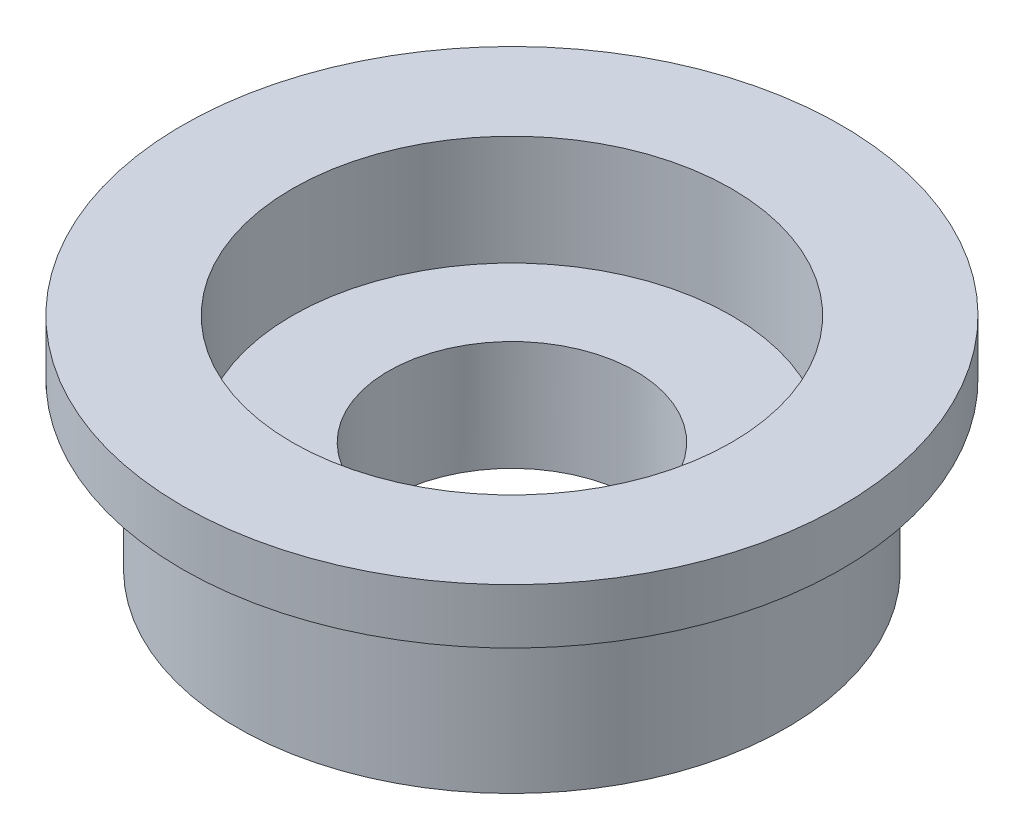
SolidWorks part; units mm, degrees
ref_plane "前视基准面" through (0, 0, 0) normal (0, 0, 1) x (1, 0, 0)
ref_plane "上视基准面" through (0, 0, 0) normal (0, 1, 0) x (1, 0, 0)
ref_plane "右视基准面" through (0, 0, 0) normal (1, 0, 0) x (0, 0, -1)
sketch "草图1" plane through (0, 0, 0) normal (0, 1, 0) x (1, 0, 0)
  circle A0 centre (0, 0) radius 6
extrude "凸台-拉伸1" add sketch "草图1" along normal blind 1
sketch "草图2" plane through (0, 0, 0) normal (0, -1, 0) x (1, 0, 0)
  circle A0 centre (0, 0) radius 5
extrude "凸台-拉伸2" add sketch "草图2" along normal blind 3
sketch "草图3" plane through (0, 1, 0) normal (0, 1, 0) x (1, 0, 0)
  circle A0 centre (0, 0) radius 4
extrude "切除-拉伸1" cut sketch "草图3" against normal blind 2
sketch "草图4" plane through (0, -1, 0) normal (0, 1, 0) x (1, 0, 0)
  circle A0 centre (0, 0) radius 2.25
extrude "切除-拉伸2" cut sketch "草图4" against normal blind 10
